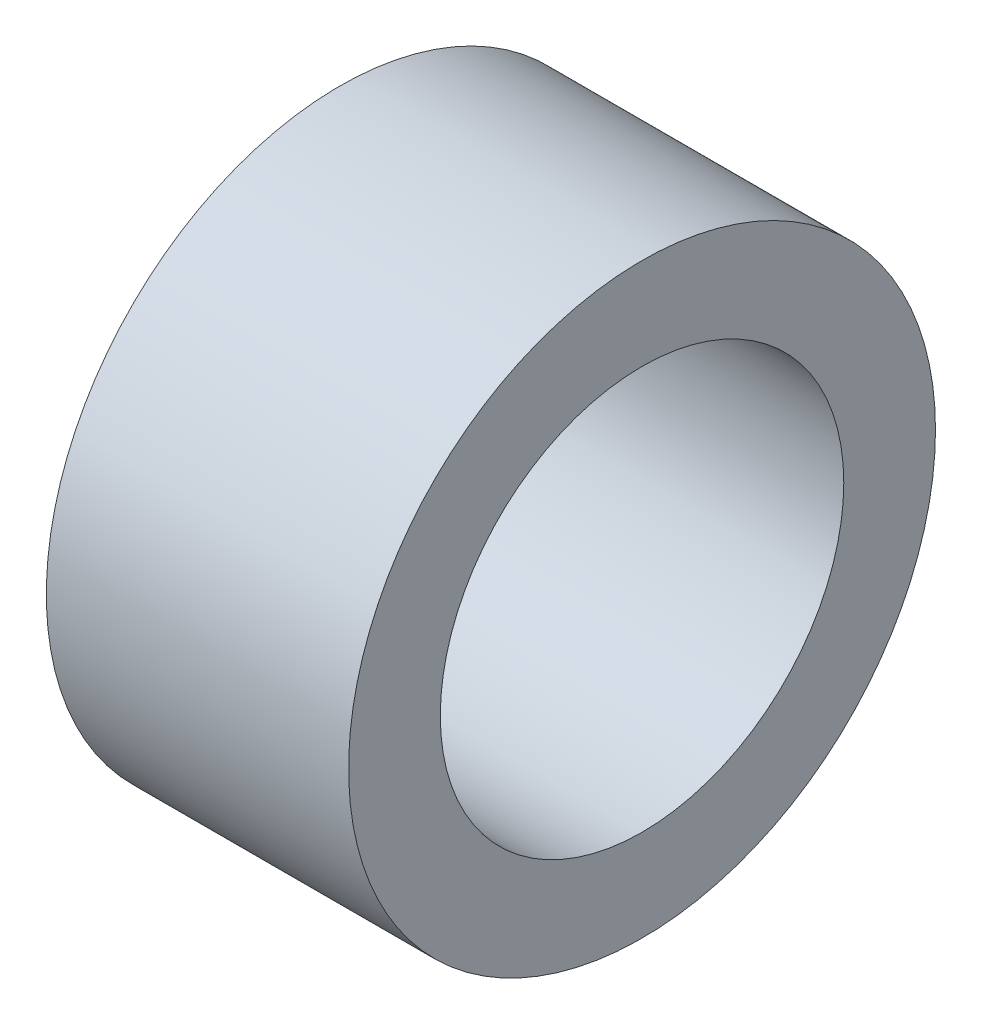
SolidWorks part; units mm, degrees
ref_plane "Front Plane" through (0, 0, 0) normal (0, 0, 1) x (1, 0, 0)
ref_plane "Top Plane" through (0, 0, 0) normal (0, 1, 0) x (1, 0, 0)
ref_plane "Right Plane" through (0, 0, 0) normal (1, 0, 0) x (0, 0, -1)
sketch "Sketch1" plane through (0, 0, 0) normal (0, 1, 0) x (1, 0, 0)
  line L0 (-19.05, 0) -> (19.05, 0)
  line L1 (15.05, 21.5) -> (15.05, -21.5)
  line L2 (-15.05, -21.5) -> (-27.05, -21.5)
  line L3 (-15.05, -21.5) -> (-15.05, 21.5)
  line L4 (-15.05, 21.5) -> (-27.05, 21.5)
  line L5 (-27.05, -21.5) -> (-27.05, 21.5)
  line L10 (4.5, -11.3898) -> (-4.5, -11.3898)
  line L11 (4.5, -11.3898) -> (4.5, 11.3898)
  line L12 (4.5, 11.3898) -> (-4.5, 11.3898)
  line L13 (-4.5, -11.3898) -> (-4.5, 11.3898)
  line L14 (4.5, -11.3898) -> (-4.5, 11.3898) construction
  line L15 (4.5, 11.3898) -> (-4.5, -11.3898) construction
  line L16 (11.05, -21.5) -> (23.05, -21.5)
  line L17 (11.05, -21.5) -> (11.05, 21.5)
  line L18 (11.05, 21.5) -> (23.05, 21.5)
  line L19 (23.05, -21.5) -> (23.05, 21.5)
  line L20 (-4.5, 6.8729) -> (-12.5, 6.8729)
  line L21 (-4.5, 6.8729) -> (-4.5, -7.6789)
  line L22 (-4.5, -7.6789) -> (-12.5, -7.6789)
  line L23 (-12.5, 6.8729) -> (-12.5, -7.6789)
  line L24 (-4.5, 6.0894) -> (-3.5, 6.0894)
  line L25 (-4.5, 6.0894) -> (-4.5, -7.0073)
  line L26 (-4.5, -7.0073) -> (-3.5, -7.0073)
  line L27 (-3.5, 6.0894) -> (-3.5, -7.0073)
  line L28 (-23.05, 21.5) -> (-23.05, -21.5)
  line L30 (-35.814, -15.5703) -> (-46.4054, -15.5703)
  line L31 (-35.814, -15.5703) -> (-35.814, 15.5703)
  line L32 (-35.814, 15.5703) -> (-46.4054, 15.5703)
  line L33 (-46.4054, -15.5703) -> (-46.4054, 15.5703)
  line L34 (-35.814, -15.5703) -> (-46.4054, 15.5703) construction
  line L35 (-35.814, 15.5703) -> (-46.4054, -15.5703) construction
  line L36 (-35.814, 15.5703) -> (-34.2265, 15.5703)
  line L37 (-35.814, 15.5703) -> (-35.814, -16.2675)
  line L38 (-35.814, -16.2675) -> (-34.2265, -16.2675)
  line L39 (-34.2265, 15.5703) -> (-34.2265, -16.2675)
  circle A0 centre (-19.05, 0) radius 2.25 construction
  circle A1 centre (19.05, 0) radius 2.25 construction
  point P9 (-15.05, 0)
  point P10 (0, 0)
  point P13 (-41.1097, 0)
  point P39 (0, 0)
  dimension "D1" = 4.5
  dimension "D2" = 38.1
  dimension "D3" = 4
  dimension "D4" = 8
  dimension "D5" = 16.764
  dimension "D6" = 9
  dimension "D7" = 8
  dimension "D8" = 4
  dimension "D9" = 8
  dimension "D10" = 1
  dimension "D11" = 4
  dimension "D12" = 43
  dimension "D13" = 4
  dimension "D14" = 1.5875
sketch "Sketch2" plane through (0, 0, 0) normal (1, 0, 0) x (0, 0, -1)
  line L0 (2.25, 0) -> (-2.25, 0) construction
  circle A0 centre (0, 0) radius 4.125
  circle A1 centre (0, 0) radius 6
  dimension "D1" = 8.25
  dimension "D2" = 12
extrude "Boss-Extrude1" add sketch "Sketch2" along normal blind 6.18
